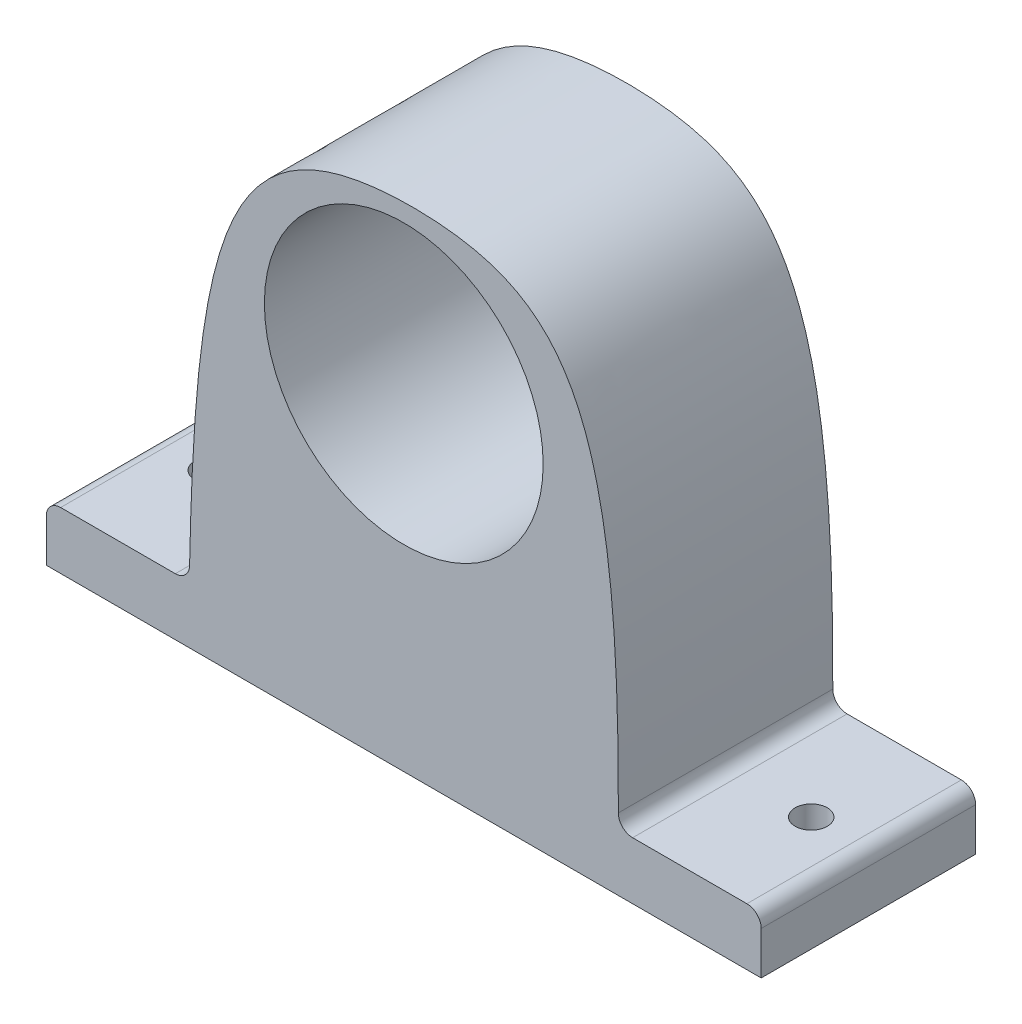
SolidWorks part; units mm, degrees
ref_plane "Front Plane" through (0, 0, 0) normal (0, 0, 1) x (1, 0, 0)
ref_plane "Top Plane" through (0, 0, 0) normal (0, 1, 0) x (1, 0, 0)
ref_plane "Right Plane" through (0, 0, 0) normal (1, 0, 0) x (0, 0, -1)
sketch "Sketch1" plane through (0, 0, 0) normal (0, 1, 0) x (1, 0, 0)
  line L1 (-50, 15) -> (50, 15)
  line L2 (-50, 15) -> (-50, -15)
  line L3 (-50, -15) -> (50, -15)
  line L4 (50, 15) -> (50, -15)
  line L5 (-50, 15) -> (50, -15) construction
  line L6 (-50, -15) -> (50, 15) construction
  point P0 (0, 0)
  dimension "D1" = 100
  dimension "D2" = 30
extrude "Boss-Extrude1" add sketch "Sketch1" along normal blind 8
sketch "Sketch2" plane through (0, 0, 15) normal (0, 0, 1) x (1, 0, 0)
  line L0 (0, 0) -> (0, 13.1444) construction
  line L1 (-50, 0) -> (50, 0) construction
  line L2 (-50, 8) -> (50, 8) construction
  line L3 (50, 8) -> (30, 8)
  line L7 (-50, 0) -> (50, 0)
  line L8 (50, 0) -> (50, 8)
  line L9 (50, 8) -> (-50, 8)
  line L10 (-50, 8) -> (-50, 0)
  line L11 (-50, 0) -> (50, 0)
  line L12 (50, 0) -> (50, 8)
  line L13 (-30, 8) -> (-50, 8)
  line L14 (-50, 8) -> (-50, 0)
  spline S0 degree 3 poles (-30, 8) (-29.2948, 47.1596) (-25.0595, 68.4938) (21.924, 69.7152) (30.4408, 55.3811) (30, 8) knots 0 0 0 0 0.475247 0.575247 1 1 1 1
  dimension "D1" = 30
  dimension "D3" = 30
  dimension "D4" = 69
  dimension "D2" = 0
extrude "Boss-Extrude2" add sketch "Sketch2" against normal up to surface (30 mm away) up to face at (0, 4, -15)
sketch "Sketch3" plane through (0, 0, 15) normal (0, 0, 1) x (1, 0, 0)
  circle A0 centre (0, 47) radius 19.5
  dimension "D1" = 39
  dimension "D2" = 47
extrude "Cut-Extrude1" cut sketch "Sketch3" against normal through all
sketch "Sketch4" plane through (0, 8, 0) normal (0, 1, 0) x (1, 0, 0)
  circle A0 centre (-42, 0) radius 2.25
  circle A1 centre (42, 0) radius 2.25
  dimension "D1" = 4.5
  dimension "D2" = 42
  dimension "D3" = 42
extrude "Cut-Extrude2" cut sketch "Sketch4" against normal through all
fillet "Fillet1" radius 2 4 edges at (-30, 8, 0) (30, 8, 0) (50, 8, 0) (-50, 8, 0)
